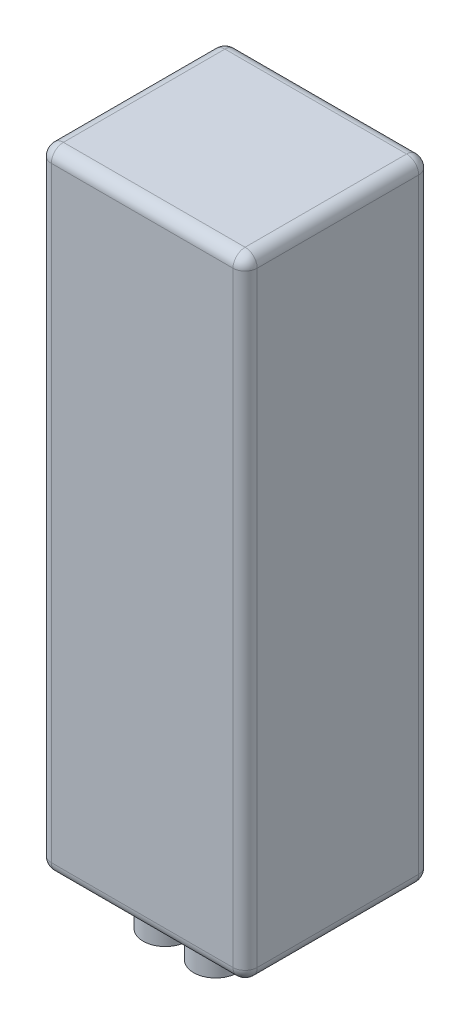
SolidWorks part; units mm, degrees
ref_plane "Front Plane" through (0, 0, 0) normal (0, 0, 1) x (1, 0, 0)
ref_plane "Top Plane" through (0, 0, 0) normal (0, 1, 0) x (1, 0, 0)
ref_plane "Right Plane" through (0, 0, 0) normal (1, 0, 0) x (0, 0, -1)
other "Center of Mass"
sketch "Sketch1" plane through (0, 0, 0) normal (0, 1, 0) x (1, 0, 0)
  line L1 (-39.4956, 20.7) -> (11.5044, 20.7)
  line L2 (-39.4956, 20.7) -> (-39.4956, -25.3)
  line L3 (-39.4956, -25.3) -> (11.5044, -25.3)
  line L4 (11.5044, 20.7) -> (11.5044, -25.3)
  dimension "D1" = 46
  dimension "D2" = 51
extrude "Boss-Extrude1" add sketch "Sketch1" along normal blind 156
fillet "Fillet1" radius 3 12 edges at (11.5044, 0, 2.3) (11.5044, 156, 2.3) (-39.4956, 156, 2.3) (-39.4956, 0, 2.3) (11.5044, 78, -20.7) (-13.9956, 156, -20.7) (-39.4956, 78, -20.7) (-13.9956, 0, -20.7) (-39.4956, 78, 25.3) (-13.9956, 156, 25.3) (11.5044, 78, 25.3) (-13.9956, 0, 25.3)
sketch "Sketch2" plane through (0, 0, 0) normal (0, -1, 0) x (1, 0, 0)
  circle A0 centre (-21.2412, 12.3253) radius 5.4797
  circle A1 centre (-8.249, 12.825) radius 5.4797
extrude "Boss-Extrude2" add sketch "Sketch2" along normal blind 10
